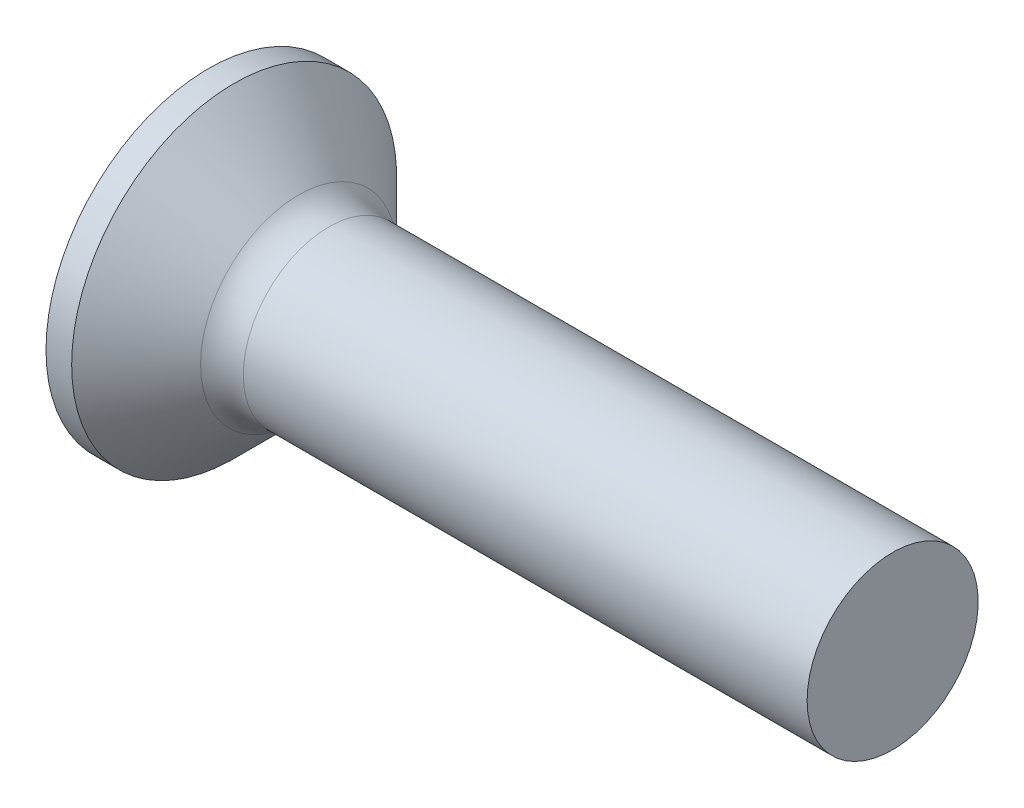
SolidWorks part; units mm, degrees
revolve "Base-Revolve" add sketch "BodySke" angle 360 about L5
sketch "BodySke" plane through (0, 0, 0) normal (0, 0, 1) x (1, 0, 0)
  line L0 (0, 0) -> (0, 1.9)
  line L1 (0, 1.9) -> (0.3, 1.9)
  line L2 (1.2, 1) -> (8, 1)
  line L3 (8, 1) -> (8, 0)
  line L4 (8, 0) -> (0, 0)
  line L5 (-6.35, 0) -> (82.55, 0) construction
  line L6 (1.2, -1) -> (8, -1) construction
  line L7 (0.3, -1.9) -> (1.2, -1) construction
  line L8 (0.3, 1.9) -> (1.2, 1)
  line L9 (0, -1.9) -> (0.3, -1.9) construction
  line L10 (1.6, 2.5875) -> (1.6, -6.9375) construction
  line L11 (0, 6.35) -> (0, -3.175) construction
  dimension "Diameter" = 2
  dimension "Length" = 8
  dimension "Head_ht" = 1.2
  dimension "Head_dia" = 3.8
  dimension "Head_ang" = 90
  dimension "D6" = 0.3
  dimension "Advance" = 0.4
  dimension "Thread_nom" = 8
cosmetic thread "ThreadCosmetic" parameters "Thread_length"=6.4, "Thread_minor"=1.548
ref_plane "Plane1" through (0, 0, 0) normal (0, 0, 1) x (1, 0, 0)
ref_plane "Plane2" through (0, 0, 0) normal (0, 1, 0) x (1, 0, 0)
ref_plane "Plane3" through (0, 0, 0) normal (1, 0, 0) x (0, 0, -1)
fillet "Fillet1" radius 0.5 1 edges at (1.2, 0, 1)
sketch "Sketch3" plane through (0, 0, 0) normal (-1, 0, 0) x (0, 0, 1)
  line L0 (-0.24, 0.95) -> (0.24, 0.95)
  line L1 (0.24, 0.95) -> (0.24, -0.95)
  line L2 (0.24, -0.95) -> (-0.24, -0.95)
  line L3 (-0.24, -0.95) -> (-0.24, 0.95)
  dimension "Cross_dia" = 1.9
  dimension "Cross_width" = 0.48
  dimension "D1" = 0.95
  dimension "D2" = 0.24
ref_plane "Plane4" through (1.2, 0, 0) normal (-1, 0, 0) x (0, 0, 1)
sketch "Sketch4" plane through (1.2, 0, 0) normal (-1, 0, 0) x (0, 0, 1)
  line L0 (-0.24, 0.3517) -> (0.24, 0.3517)
  line L3 (0.24, 0.3517) -> (0.24, -0.3517)
  line L4 (0.24, -0.3517) -> (-0.24, -0.3517)
  line L5 (-0.24, -0.3517) -> (-0.24, 0.3517)
  dimension "D2" = 0.7034
  dimension "D1" = 0.48
  dimension "D4" = 0.3517
  dimension "D3" = 0.24
loft "Recess" cut profiles "Sketch3", "Sketch4"
pattern_circular "RecPat" count 2 every 90 about axis through (0, 0, 0) along (1, 0, 0) of "Recess"
sketch "RecCorSke" plane through (0, 0, 0) normal (0, 0, 1) x (1, 0, 0)
  line L0 (-3.175, 0) -> (15.875, 0) construction
  line L2 (0, 0) -> (0, 0.4394)
  line L3 (0, 0.4394) -> (1.2, 0.3555)
  line L4 (1.2, 0.3555) -> (1.3155, 0)
  line L5 (1.3155, 0) -> (0, 0)
  dimension "Diameter" = 0.711
  dimension "Depth" = 1.2
  dimension "Draft_angle" = 4
  dimension "Bottom_angle" = 18
revolve "RecessCore" cut sketch "RecCorSke" angle 360 about L0
sketch "ThdSchSke" plane through (0, 0, 0) normal (0, 0, 1) x (1, 0, 0)
  line L0 (1.6, -0.774) -> (1.4418, -1)
  line L1 (1.6, -0.774) -> (1.7582, -1)
  line L2 (1.7582, -1) -> (1.7582, -1.25)
  line L3 (-3.175, 0) -> (5.1513, 0) construction
  line L5 (1.7582, -1.25) -> (1.4418, -1.25)
  line L6 (1.4418, -1.25) -> (1.4418, -1)
  line L7 (0, 1.9) -> (0, -1.9) construction
  dimension "Diameter" = 2
  dimension "Thread_minor" = 1.548
  dimension "Start" = 1.6
revolve "ThreadSchematic" [suppressed] cut sketch "ThdSchSke" angle 360 about L3
pattern_linear "ThdSchPat" [suppressed]
equation "\"D1@Sketch3\" = \"Cross_dia@Sketch3\" / 2"
equation "\"D2@Sketch3\" = \"Cross_width@Sketch3\" / 2"
equation "\"Depth@RecCorSke\" = \"Cross_depth@Plane4\""
equation "\"D1@Sketch4\" = \"Cross_width@Sketch3\""
equation "\"D2@Sketch4\" = \"Cross_dia@Sketch3\" - 2.0 * \"Cross_depth@Plane4\" * tan(26.5  * 0.017453292)"
equation "\"D3@Sketch4\" = \"D1@Sketch4\" / 2"
equation "\"D4@Sketch4\" = \"D2@Sketch4\" / 2"
equation "\"Thread_length@ThreadCosmetic\" = ((sgn( (\"Length@BodySke\" - \"Advance@BodySke\" * 1.0 - \"Head_ht@BodySke\" ) - \"Thread_nom@BodySke\" )-1)*( (\"Length@BodySke\" - \"Advance@BodySke\" * 1.0 - \"Head_ht@BodySke\" ) - \"Thread_nom@BodySke\" ))/-2+ \"Thread_nom@BodySke\""
equation "\"Thread_minor@ThdSchSke\" = \"Thread_minor@ThreadCosmetic\""
equation "\"Diameter@ThdSchSke\" = \"Diameter@BodySke\""
equation "\"Overcut@ThdSchSke\" = \"Diameter@BodySke\" * 1.25"
equation "\"Start@ThdSchSke\" = 0.000001 + \"Length@BodySke\" - \"Thread_length@ThreadCosmetic\"  '---Countersunk---"
equation "\"Num_threads@ThdSchPat\" = int( \"Thread_length@ThreadCosmetic\" / \"Advance@BodySke\" + 0.999 )  + 1"
equation "\"Advance@ThdSchPat\" = \"Thread_length@ThreadCosmetic\" /  (\"Num_threads@ThdSchPat\" - 1) 'relax it"
